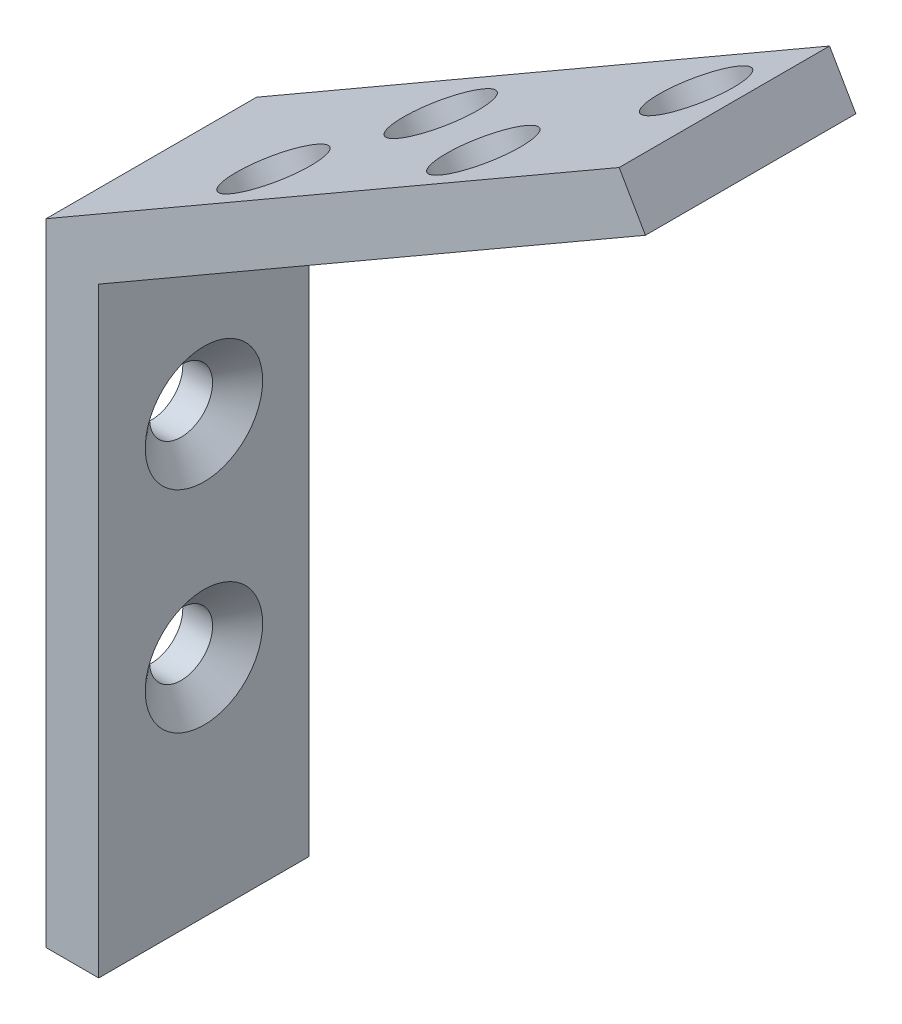
SolidWorks part; units mm, degrees
ref_plane "Front Plane" through (0, 0, 0) normal (0, 0, 1) x (1, 0, 0)
ref_plane "Top Plane" through (0, 0, 0) normal (0, 1, 0) x (1, 0, 0)
ref_plane "Right Plane" through (0, 0, 0) normal (1, 0, 0) x (0, 0, -1)
sketch "Sketch1" plane through (0, 0, 0) normal (0, 0, 1) x (1, 0, 0)
  line L0 (-1.5875, 19.05) -> (32.9956, 39.0165)
  line L1 (-1.5875, -19.05) -> (1.5875, -19.05)
  line L2 (-1.5875, -19.05) -> (-1.5875, 19.05)
  line L4 (1.5875, -19.05) -> (1.5875, 17.2169)
  line L5 (-1.5875, 0) -> (0, 0) construction
  line L6 (-1.5875, 19.05) -> (1.5875, -19.05) construction
  line L7 (32.9956, 39.0165) -> (34.5831, 36.2669)
  line L8 (34.5831, 36.2669) -> (1.5875, 17.2169)
  line L9 (0, 0) -> (1.5875, 0) construction
  point P0 (0, 0)
  point P10 (0, 0)
  point P12 (0, 0)
  point P13 (0, 0)
  point P14 (0, 0)
  dimension "D1" = 3.175
  dimension "D2" = 38.1
  dimension "D3" = 120
  dimension "D4" = 38.1
  dimension "D5" = 3.175
extrude "Boss-Extrude1" add sketch "Sketch1" along normal blind 12.7
hole_wizard "CSK for #6 Flat Head Machine Screw (100)1" positions "Sketch2" profile "Sketch3" countersink size "#6" standard "ANSI Inch"
sketch "Sketch2" plane through (1.5875, 0, 0) normal (1, 0, 0) x (0, 0, -1)
  line L0 (-6.35, 17.2169) -> (-6.35, -19.05) construction
  line L1 (-12.7, 17.2169) -> (0, 17.2169) construction
  line L2 (-12.7, -19.05) -> (0, -19.05) construction
  point P0 (-6.35, 7.2479)
  point P2 (-6.35, -5.4637)
  point P13 (-6.35, 7.2479)
  point P14 (-6.35, -5.4637)
sketch "Sketch3" plane through (1.5875, 7.2479, 6.35) normal (0, 1, 0) x (0, 0, -1)
  line L0 (0, 0) -> (0, 13.8408)
  line L1 (0, 13.8408) -> (1.8986, 12.7)
  line L2 (1.8986, 12.7) -> (1.8986, 1.38)
  line L3 (1.8986, 1.38) -> (3.5433, 0)
  line L5 (3.5433, 0) -> (0, 0)
  line L6 (-1.8986, 1.38) -> (-3.5433, 0) construction
  line L10 (0, 13.8408) -> (-1.8986, 12.7) construction
  line L11 (0, -6.35) -> (0, 107.95) construction
  dimension "Hole Dia." = 3.7973
  dimension "Hole Depth" = 12.7
  dimension "Near C'Sink Dia." = 7.0866
  dimension "Near C'Sink Angle" = 100
  dimension "Drill Angle" = 118
hole_wizard "#6 (0.204) Diameter Hole1" positions "Sketch6" profile "Sketch7" hole size "#6" standard "ANSI Inch"
sketch "Sketch6" plane through (-7.0583, 12.2253, 0) normal (0.5, -0.866, 0) x (-0.866, -0.5, 0)
  point P0 (-43.4765, -4.0667)
  point P2 (-34.423, -9.0688)
  point P4 (-25.6803, -4.0667)
  point P6 (-19.7988, -9.0688)
  point P9 (-25.6803, -4.0667)
  point P10 (-34.423, -9.0688)
  point P11 (-43.4765, -4.0667)
  point P12 (-19.7988, -9.0688)
sketch "Sketch7" plane through (30.5935, 33.9635, 4.0667) normal (0, 0, 1) x (0.866, 0.5, 0)
  line L0 (0, 0) -> (0, 14.2567)
  line L1 (0, 14.2567) -> (2.5908, 12.7)
  line L2 (2.5908, 12.7) -> (2.5908, 0)
  line L5 (2.5908, 0) -> (0, 0)
  line L10 (0, 14.2567) -> (-2.5908, 12.7) construction
  line L11 (0, -6.35) -> (0, 107.95) construction
  dimension "Hole Dia." = 5.1816
  dimension "Hole Depth" = 12.7
  dimension "Drill Angle" = 118
